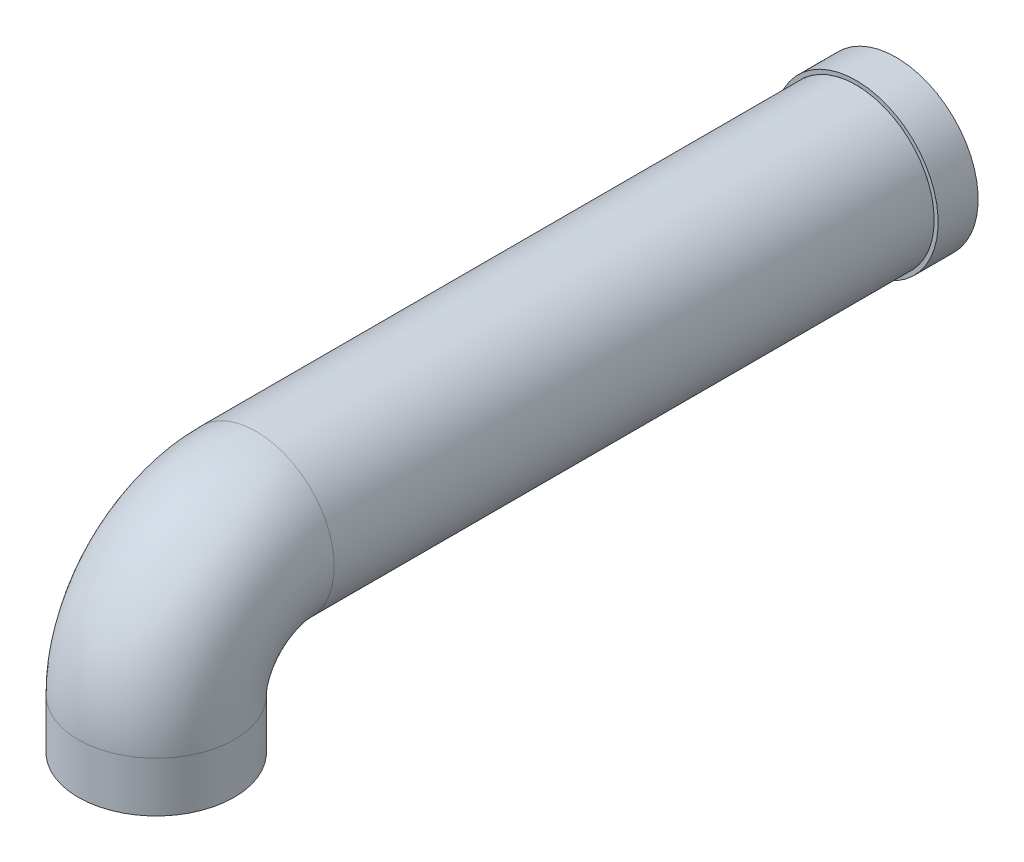
SolidWorks part; units mm, degrees
ref_plane "Front Plane" through (0, 0, 0) normal (0, 0, 1) x (1, 0, 0)
ref_plane "Top Plane" through (0, 0, 0) normal (0, 1, 0) x (1, 0, 0)
ref_plane "Right Plane" through (0, 0, 0) normal (1, 0, 0) x (0, 0, -1)
sketch "Sketch2" plane through (0, 0, 0) normal (1, 0, 0) x (0, 0, -1)
  line L0 (0, 0) -> (0, 25)
  line L1 (50, 75) -> (350, 75)
  arc A0 (0, 25) -> (50, 75) centre (50, 25) cw
  point P6 (0, 75)
  dimension "D3" = 50
  dimension "D1" = 75
  dimension "D2" = 350
sketch "Sketch3" plane through (0, 0, 0) normal (0, 1, 0) x (1, 0, 0)
  circle A0 centre (0, 0) radius 39
sweep "Sweep2" add path "Sketch2" circular profile diameter 78 parameters "D3"=78
sketch "Sketch8" plane through (0, 0, -350) normal (0, 0, -1) x (-1, 0, 0)
  circle A0 centre (0, 75) radius 41
  circle A1 centre (0, 75) radius 39
  dimension "D1" = 82
  dimension "D2" = 78
extrude "Boss-Extrude1" add sketch "Sketch8" along normal blind 20 separate body
sketch "Sketch11" plane through (0, 0, -350) normal (0, 0, -1) x (-1, 0, 0)
  circle A0 centre (0, 75) radius 25
extrude "Cut-Extrude1" cut sketch "Sketch11" against normal blind 300
